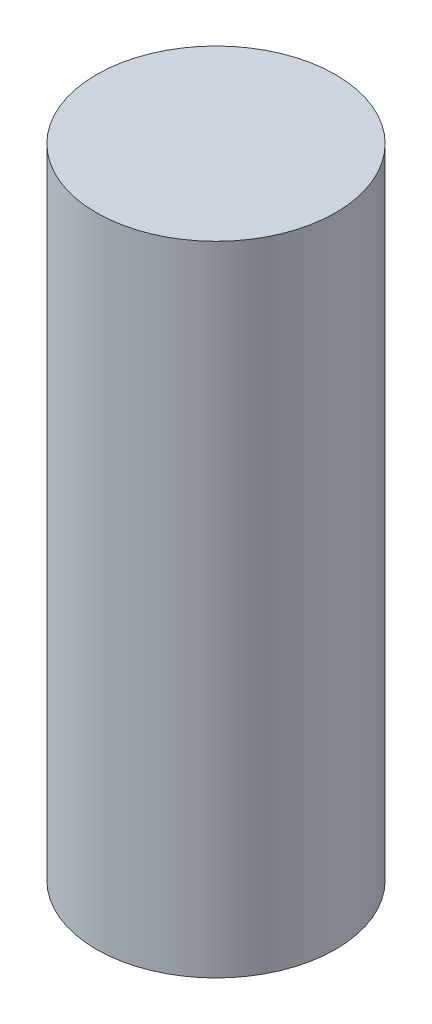
SolidWorks part; units mm, degrees
ref_plane "Front Plane" through (0, 0, 0) normal (0, 0, 1) x (1, 0, 0)
ref_plane "Top Plane" through (0, 0, 0) normal (0, 1, 0) x (1, 0, 0)
ref_plane "Right Plane" through (0, 0, 0) normal (1, 0, 0) x (0, 0, -1)
sketch "Sketch1" plane through (0, 0, 0) normal (0, 1, 0) x (1, 0, 0)
  circle A0 centre (0, 0) radius 9.525
  dimension "D1" = 19.05
extrude "Boss-Extrude1" add sketch "Sketch1" along normal blind 50.8
